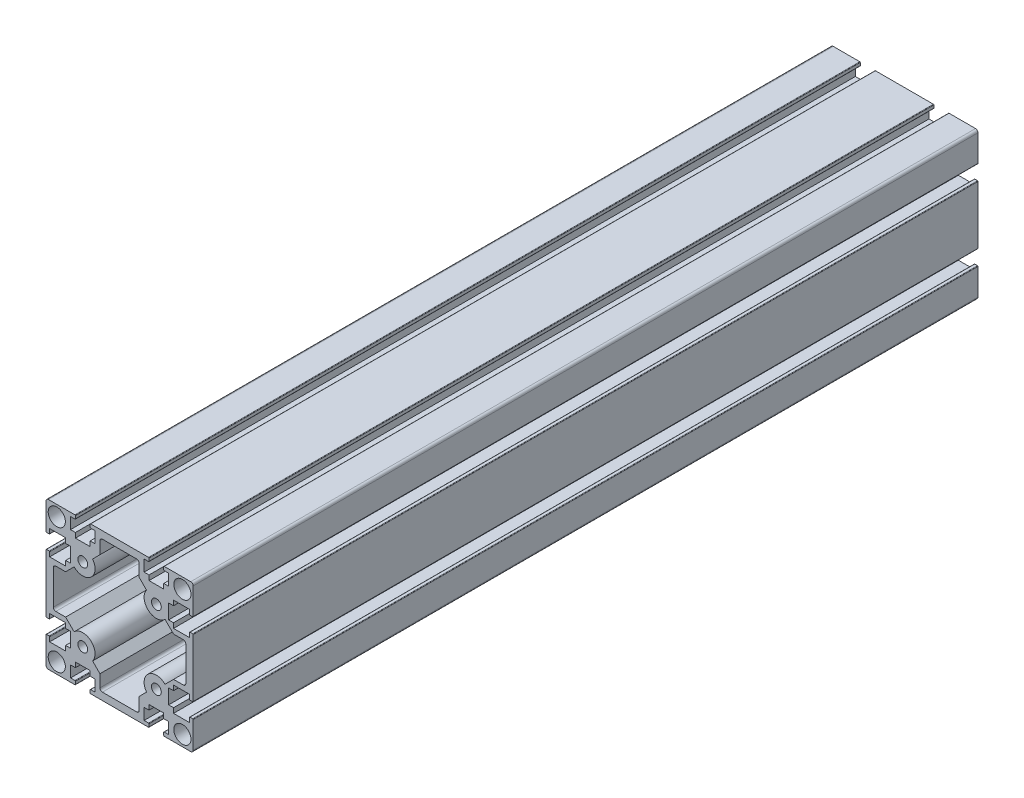
SolidWorks part; units mm, degrees
ref_plane "Front Plane" through (0, 0, 0) normal (0, 0, 1) x (1, 0, 0)
ref_plane "Top Plane" through (0, 0, 0) normal (0, 1, 0) x (1, 0, 0)
ref_plane "Right Plane" through (0, 0, 0) normal (1, 0, 0) x (0, 0, -1)
sketch "Sketch1" plane through (0, 0, 0) normal (0, 0, 1) x (1, 0, 0)
  line L0 (-65.4467, 0) -> (65.4467, 0) construction
  line L1 (-15, -15) -> (15, -15) construction
  line L2 (-15, -15) -> (-15, 14) construction
  line L3 (-14, 15) -> (15, 15) construction
  line L4 (15, -15) -> (15, 15) construction
  line L5 (-15, -15) -> (15, 15) construction
  line L6 (-15, 15) -> (15, -15) construction
  line L7 (-5, 3) -> (-5, -3)
  line L8 (-5, 3) -> (-7, 3)
  line L9 (-7, 3) -> (-7, 5)
  line L10 (-7, 5) -> (-13.5, 5)
  line L11 (-13.5, 5) -> (-13.5, 3)
  line L12 (-13.5, 3) -> (-15, 3)
  line L13 (-15, 3) -> (-15, 14)
  line L14 (-14, 15) -> (-3, 15)
  line L15 (-3, 15) -> (-3, 13.5)
  line L16 (-3, 13.5) -> (-5, 13.5)
  line L17 (-5, 13.5) -> (-5, 8.8744)
  line L18 (-5, 8.8744) -> (-3, 8.8744)
  line L19 (0, 0) -> (0, 16.9147) construction
  line L20 (-3, 8.8744) -> (-3, 6.8744)
  line L21 (-3, 6.8744) -> (3, 6.8744)
  line L22 (3, 8.8744) -> (3, 6.8744)
  line L23 (5, 8.8744) -> (3, 8.8744)
  line L24 (3, 13.5) -> (5, 13.5)
  line L25 (5, 13.5) -> (5, 8.8744)
  line L26 (3, 15) -> (3, 13.5)
  line L27 (3, 15) -> (27, 15)
  line L28 (7, 6) -> (4, 3)
  line L29 (7, 6) -> (7, 11)
  line L30 (8, 12) -> (22, 12)
  line L31 (-5, -3) -> (-7, -3)
  line L32 (-7, -3) -> (-7, -5)
  line L33 (-13.5, -3) -> (-15, -3)
  line L34 (-13.5, -5) -> (-13.5, -3)
  line L35 (-7, -5) -> (-13.5, -5)
  line L36 (-15, -3) -> (-15, -27)
  line L37 (-12, -22) -> (-12, -8)
  line L38 (-11, -7) -> (-7, -7)
  line L39 (-7, -7) -> (-3.5355, -3.5355)
  line L40 (7, -36) -> (4, -33)
  line L41 (7, -36) -> (7, -41)
  line L42 (8, -42) -> (22, -42)
  line L43 (3, -45) -> (27, -45)
  line L44 (3, -45) -> (3, -43.5)
  line L45 (3, -43.5) -> (5, -43.5)
  line L46 (5, -43.5) -> (5, -38.8744)
  line L47 (5, -38.8744) -> (3, -38.8744)
  line L48 (3, -38.8744) -> (3, -36.8744)
  line L49 (-3, -36.8744) -> (3, -36.8744)
  line L50 (-3, -38.8744) -> (-3, -36.8744)
  line L51 (-5, -38.8744) -> (-3, -38.8744)
  line L52 (-5, -43.5) -> (-5, -38.8744)
  line L53 (-3, -43.5) -> (-5, -43.5)
  line L54 (-3, -45) -> (-3, -43.5)
  line L55 (-14, -45) -> (-3, -45)
  line L56 (-15, -33) -> (-15, -44)
  line L57 (-13.5, -33) -> (-15, -33)
  line L58 (-13.5, -35) -> (-13.5, -33)
  line L59 (-7, -35) -> (-13.5, -35)
  line L60 (-7, -33) -> (-7, -35)
  line L61 (-5, -33) -> (-7, -33)
  line L62 (-5, -33) -> (-5, -27)
  line L63 (-5, -27) -> (-7, -27)
  line L64 (-7, -27) -> (-7, -25)
  line L65 (-7, -23) -> (-3.5355, -26.4645)
  line L66 (-13.5, -27) -> (-15, -27)
  line L67 (-13.5, -25) -> (-13.5, -27)
  line L68 (-7, -25) -> (-13.5, -25)
  line L69 (-11, -23) -> (-7, -23)
  line L70 (23, 6) -> (26, 3)
  line L71 (23, 6) -> (23, 11)
  line L72 (27, 15) -> (27, 13.5)
  line L73 (27, 13.5) -> (25, 13.5)
  line L74 (25, 13.5) -> (25, 8.8744)
  line L75 (25, 8.8744) -> (27, 8.8744)
  line L76 (27, 8.8744) -> (27, 6.8744)
  line L77 (33, 6.8744) -> (27, 6.8744)
  line L78 (33, 8.8744) -> (33, 6.8744)
  line L79 (35, 8.8744) -> (33, 8.8744)
  line L80 (35, 13.5) -> (35, 8.8744)
  line L81 (33, 13.5) -> (35, 13.5)
  line L82 (33, 15) -> (33, 13.5)
  line L83 (44, 15) -> (33, 15)
  line L84 (45, 3) -> (45, 14)
  line L85 (43.5, 3) -> (45, 3)
  line L86 (43.5, 5) -> (43.5, 3)
  line L87 (37, 5) -> (43.5, 5)
  line L88 (37, 3) -> (37, 5)
  line L89 (35, 3) -> (37, 3)
  line L90 (35, -3) -> (37, -3)
  line L91 (35, 3) -> (35, -3)
  line L92 (37, -7) -> (33.5355, -3.5355)
  line L93 (37, -3) -> (37, -5)
  line L94 (43.5, -3) -> (45, -3)
  line L95 (43.5, -5) -> (43.5, -3)
  line L96 (37, -5) -> (43.5, -5)
  line L97 (41, -7) -> (37, -7)
  line L98 (42, -22) -> (42, -8)
  line L99 (41, -23) -> (37, -23)
  line L100 (45, -3) -> (45, -27)
  line L101 (43.5, -27) -> (45, -27)
  line L102 (43.5, -25) -> (43.5, -27)
  line L103 (37, -25) -> (43.5, -25)
  line L104 (37, -23) -> (33.5355, -26.4645)
  line L105 (37, -27) -> (37, -25)
  line L106 (35, -27) -> (37, -27)
  line L107 (23, -36) -> (26, -33)
  line L108 (35, -33) -> (35, -27)
  line L109 (35, -33) -> (37, -33)
  line L110 (37, -33) -> (37, -35)
  line L111 (43.5, -33) -> (45, -33)
  line L112 (43.5, -35) -> (43.5, -33)
  line L113 (37, -35) -> (43.5, -35)
  line L114 (45, -33) -> (45, -44)
  line L115 (44, -45) -> (33, -45)
  line L116 (33, -45) -> (33, -43.5)
  line L117 (33, -43.5) -> (35, -43.5)
  line L118 (35, -43.5) -> (35, -38.8744)
  line L119 (35, -38.8744) -> (33, -38.8744)
  line L120 (33, -38.8744) -> (33, -36.8744)
  line L121 (33, -36.8744) -> (27, -36.8744)
  line L122 (27, -38.8744) -> (27, -36.8744)
  line L123 (25, -38.8744) -> (27, -38.8744)
  line L124 (23, -36) -> (23, -41)
  line L125 (25, -43.5) -> (25, -38.8744)
  line L126 (27, -43.5) -> (25, -43.5)
  line L127 (27, -45) -> (27, -43.5)
  circle A0 centre (0, 0) radius 2
  arc A1 (-3.5355, -3.5355) -> (4, 3) centre (0, 0) ccw
  circle A2 centre (-10.6066, 10.6066) radius 3.5
  arc A3 (-15, 14) -> (-14, 15) centre (-14, 14) cw
  arc A4 (7, 11) -> (8, 12) centre (8, 11) cw
  arc A5 (-12, -8) -> (-11, -7) centre (-11, -8) cw
  arc A6 (7, -41) -> (8, -42) centre (8, -41) ccw
  arc A7 (-15, -44) -> (-14, -45) centre (-14, -44) ccw
  circle A8 centre (-10.6066, -40.6066) radius 3.5
  arc A9 (-3.5355, -26.4645) -> (4, -33) centre (0, -30) cw
  arc A10 (-12, -22) -> (-11, -23) centre (-11, -22) ccw
  circle A11 centre (0, -30) radius 2
  arc A12 (23, 11) -> (22, 12) centre (22, 11) ccw
  circle A13 centre (40.6066, 10.6066) radius 3.5
  arc A14 (45, 14) -> (44, 15) centre (44, 14) ccw
  circle A15 centre (30, 0) radius 2
  arc A16 (33.5355, -3.5355) -> (26, 3) centre (30, 0) cw
  arc A17 (42, -8) -> (41, -7) centre (41, -8) ccw
  arc A18 (42, -22) -> (41, -23) centre (41, -22) cw
  arc A19 (33.5355, -26.4645) -> (26, -33) centre (30, -30) ccw
  circle A20 centre (30, -30) radius 2
  arc A21 (45, -44) -> (44, -45) centre (44, -44) cw
  circle A22 centre (40.6066, -40.6066) radius 3.5
  arc A23 (23, -41) -> (22, -42) centre (22, -41) cw
  point P0 (0, 0)
  point P9 (0, 0)
  point P33 (0, 6.8744)
  point P96 (-12, -15)
  point P102 (15, 12)
  point P176 (15, -42)
  point P179 (15, -45)
  dimension "D3" = 4
  dimension "D4" = 10
  dimension "D11" = 7
  dimension "D13" = 1
  dimension "D22" = 1
  dimension "D25" = 1
  dimension "D1" = 30
  dimension "D2" = 30
  dimension "D5" = 6
  dimension "D7" = 2
  dimension "D8" = 2
  dimension "D9" = 6.5
  dimension "D10" = 2
  dimension "D12" = 15
  dimension "D14" = 1.5
  dimension "D15" = 5
  dimension "D16" = 2
  dimension "D17" = 3
  dimension "D18" = 3
  dimension "D19" = 3
  dimension "D21" = 2
  dimension "D23" = 3
  dimension "D24" = 2
extrude "Boss-Extrude1" add sketch "Sketch1" along normal blind 320
fillet "Fillet1" radius 0.2 16 edges at (-3, -45, 160) (3, -45, 160) (27, -45, 160) (33, -45, 160) (-15, 3, 160) (-15, -3, 160) (-15, -27, 160) (-15, -33, 160) (45, -33, 160) (45, -27, 160) (45, -3, 160) (45, 3, 160) (27, 15, 160) (-3, 15, 160) (3, 15, 160) (33, 15, 160)
fillet "Fillet2" radius 0.2 16 edges at (-13.5, 3, 160) (43.5, 3, 160) (43.5, -3, 160) (43.5, -27, 160) (43.5, -33, 160) (33, -43.5, 160) (27, -43.5, 160) (3, -43.5, 160) (-3, -43.5, 160) (-13.5, -33, 160) (-13.5, -27, 160) (-13.5, -3, 160) (-3, 13.5, 160) (3, 13.5, 160) (27, 13.5, 160) (33, 13.5, 160)
sketch "Sketch2" plane through (0, 15, 0) normal (0, 1, 0) x (1, 0, 0)
  line L0 (15, 0) -> (15, -173.8062) construction
  line L1 (26.8, 0) -> (3.2, 0) construction
  line L3 (5, -105) -> (25, -105)
  line L4 (5, -105) -> (5, -75)
  line L5 (5, -75) -> (25, -75)
  line L6 (25, -105) -> (25, -75)
  line L7 (5, -105) -> (25, -75) construction
  line L8 (5, -75) -> (25, -105) construction
  point P4 (15, -90)
  dimension "D1" = 30
  dimension "D2" = 20
  dimension "D3" = 75
